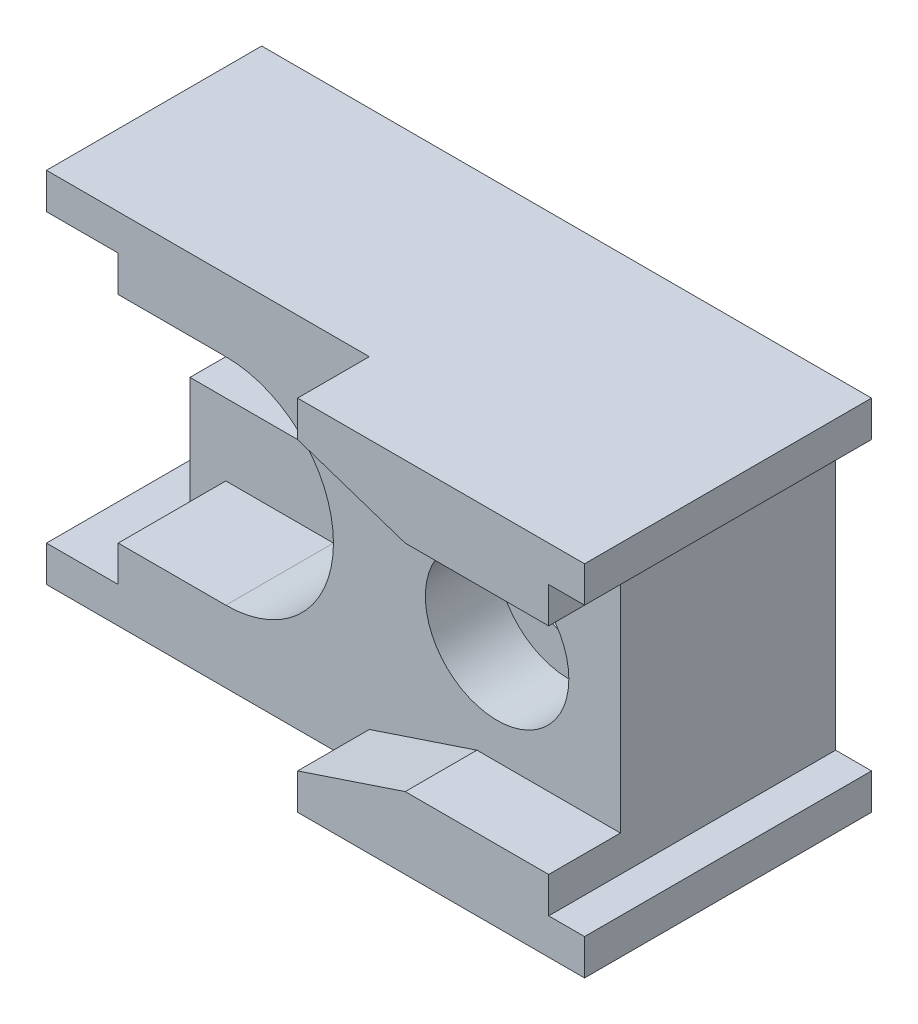
SolidWorks part; units mm, degrees
ref_plane "Front" through (0, 0, 0) normal (0, 0, 1) x (1, 0, 0)
ref_plane "Top" through (0, 0, 0) normal (0, 1, 0) x (1, 0, 0)
ref_plane "Right" through (0, 0, 0) normal (1, 0, 0) x (0, 0, -1)
sketch "Sketch1" plane through (0, 0, 0) normal (0, 0, 1) x (1, 0, 0)
  line L0 (8.5, 4) -> (8.5, 5)
  line L1 (-8.5, -5) -> (8.5, -5)
  line L2 (-8.5, -5) -> (-8.5, -4)
  line L3 (-8.5, 5) -> (8.5, 5)
  line L4 (8.5, -5) -> (8.5, -4)
  line L5 (-8.5, -5) -> (8.5, 5) construction
  line L6 (-8.5, 5) -> (8.5, -5) construction
  line L7 (8.5, 4) -> (7.5, 4)
  line L9 (8.5, -4) -> (7.5, -4)
  line L10 (7.5, 4) -> (7.5, -4)
  line L11 (-7.5, 1) -> (-3.5, 1)
  line L12 (-7.5, -1) -> (-3.5, -1)
  line L13 (-8.5, 4) -> (-8.5, 5)
  line L14 (-8.5, 4) -> (-7.5, 4)
  line L16 (-8.5, -4) -> (-7.5, -4)
  line L17 (-7.5, 4) -> (-7.5, 1)
  line L19 (-7.5, -1) -> (-7.5, -4)
  arc A1 (-3.5, -1) -> (-3.5, 1) centre (-3.5, 0) ccw
  point P0 (0, 0)
  point P12 (-6, 0)
  dimension "D6" = 1
  dimension "D1" = 10
  dimension "D2" = 17
  dimension "D3" = 1
  dimension "D4" = 1
  dimension "D5" = 1
  dimension "D7" = 1
  dimension "D8" = 1
extrude "Boss-Extrude1" add sketch "Sketch1" along normal blind 8
sketch "Sketch3" plane through (0, 0, 8) normal (0, 0, 1) x (1, 0, 0)
  line L0 (8.5, 5) -> (8.5, 4)
  line L1 (8.5, 4) -> (7.5, 4)
  line L2 (7.5, 4) -> (7.5, 3)
  line L3 (7.5, 3) -> (3.5, 3)
  line L4 (3.5, 3) -> (0.5, 4)
  line L5 (0.5, 4) -> (0.5, 5)
  line L6 (8.5, 5) -> (-8.5, 5) construction
  line L7 (0.5, 5) -> (8.5, 5)
  line L8 (0, 0) -> (1.925, 0) construction
  line L9 (0.5, -4) -> (0.5, -5)
  line L10 (3.5, -3) -> (0.5, -4)
  line L11 (7.5, -3) -> (3.5, -3)
  line L12 (7.5, -4) -> (7.5, -3)
  line L13 (8.5, -4) -> (7.5, -4)
  line L14 (8.5, -5) -> (8.5, -4)
  line L15 (0.5, -5) -> (8.5, -5)
  dimension "D1" = 1
  dimension "D2" = 3
  dimension "D3" = 1
  dimension "D4" = 4
extrude "Cut-Extrude1" cut sketch "Sketch3" against normal blind 2
sketch "Sketch4" plane through (0, 0, 6) normal (0, 0, 1) x (1, 0, 0)
  circle A0 centre (4.062, 0) radius 2
  dimension "D1" = 4
extrude "Cut-Extrude2" cut sketch "Sketch4" against normal blind 2
sketch "Sketch5" plane through (0, 0, 4) normal (0, 0, 1) x (1, 0, 0)
  circle A0 centre (4.062, 0) radius 1
  dimension "D1" = 2
extrude "Cut-Extrude3" cut sketch "Sketch5" against normal blind 22
sketch "Sketch6" plane through (0, 0, 6) normal (0, 0, 1) x (1, 0, 0)
  line L0 (-8.5, 0) -> (-3.5, 0) construction
  line L1 (-8.5, 3) -> (-7.5, 3)
  line L2 (-8.5, -3) -> (-7.5, -3)
  line L3 (-6.5, 3) -> (-6.5, 4)
  line L4 (-6.5, 4) -> (-7.5, 4)
  line L5 (-7.5, 4) -> (-7.5, -4)
  line L6 (-7.5, -1) -> (-7.5, -4) construction
  line L7 (-7.5, -4) -> (-6.5, -4)
  line L8 (-6.5, -3) -> (-6.5, -4)
  line L9 (-6.5, 3) -> (-3.5, 3)
  line L10 (-6.5, -3) -> (-3.5, -3)
  arc A0 (-8.5, 3) -> (-8.5, -3) centre (-8.5, 0) ccw
  arc A1 (-3.5, -3) -> (-3.5, 3) centre (-3.5, 0) ccw
  point P3 (-6, 0)
  dimension "D2" = 3
  dimension "D1" = 5
  dimension "D3" = 1
  dimension "D4" = 1
  dimension "D5" = 1
extrude "Cut-Extrude4" cut sketch "Sketch6" against normal blind 3
